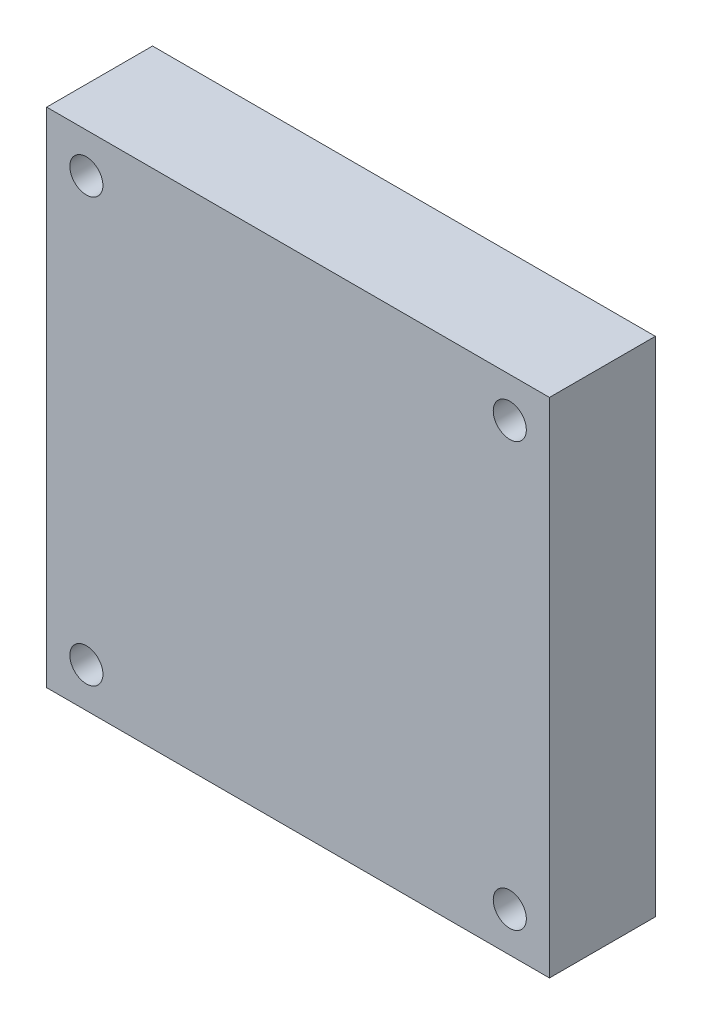
SolidWorks part; units mm, degrees
ref_plane "Front Plane" through (0, 0, 0) normal (0, 0, 1) x (1, 0, 0)
ref_plane "Top Plane" through (0, 0, 0) normal (0, 1, 0) x (1, 0, 0)
ref_plane "Right Plane" through (0, 0, 0) normal (1, 0, 0) x (0, 0, -1)
sketch "Sketch4" plane through (0, 0, 0) normal (0, 0, 1) x (1, 0, 0)
  line L0 (13, -13) -> (13, 13)
  line L1 (10, -10) -> (-10, -10)
  line L2 (10, -10) -> (10, 10)
  line L3 (10, 10) -> (-10, 10)
  line L4 (-10, -10) -> (-10, 10)
  line L5 (10, -10) -> (-10, 10) construction
  line L6 (10, 10) -> (-10, -10) construction
  line L7 (13, 13) -> (-13, 13)
  line L8 (-13, -13) -> (-13, 13)
  line L9 (13, -13) -> (-13, -13)
  point P0 (0, 0)
  dimension "D1" = 20
  dimension "D2" = 20
  dimension "D3" = 3
sketch "Sketch1" plane through (0, 0, 0) normal (0, 0, 1) x (1, 0, 0)
  line L0 (13, -13) -> (13, 13) construction
  line L1 (-19, -19) -> (19, -19)
  line L2 (-19, -19) -> (-19, 19)
  line L3 (-19, 19) -> (19, 19)
  line L4 (19, -19) -> (19, 19)
  line L5 (-19, -19) -> (19, 19) construction
  line L6 (-19, 19) -> (19, -19) construction
  line L7 (13, 13) -> (-13, 13) construction
  point P0 (0, 0)
  dimension "D1" = 6
  dimension "D2" = 6
extrude "Boss-Extrude1" add sketch "Sketch1" along normal mid plane 8
sketch "Sketch2" plane through (0, 0, 4) normal (0, 0, 1) x (1, 0, 0)
  line L0 (-19, 19) -> (-19, -19) construction
  line L1 (19, 19) -> (-19, 19) construction
  circle A0 centre (-16, 16) radius 1.25
  dimension "D2" = 2.5
  dimension "D3" = 3
  dimension "D1" = 3
extrude "Cut-Extrude1" cut sketch "Sketch2" against normal through all
mirror "Mirror1" about plane through (0, 0, 0) normal (0, 1, 0) of "Cut-Extrude1"
mirror "Mirror2" about plane through (0, 0, 0) normal (1, 0, 0) of "Mirror1", "Cut-Extrude1"
equation "\"D3@Sketch2\" = \"D1@Sketch2\""
equation "\"D2@Sketch1\"=\"D1@Sketch1\""
